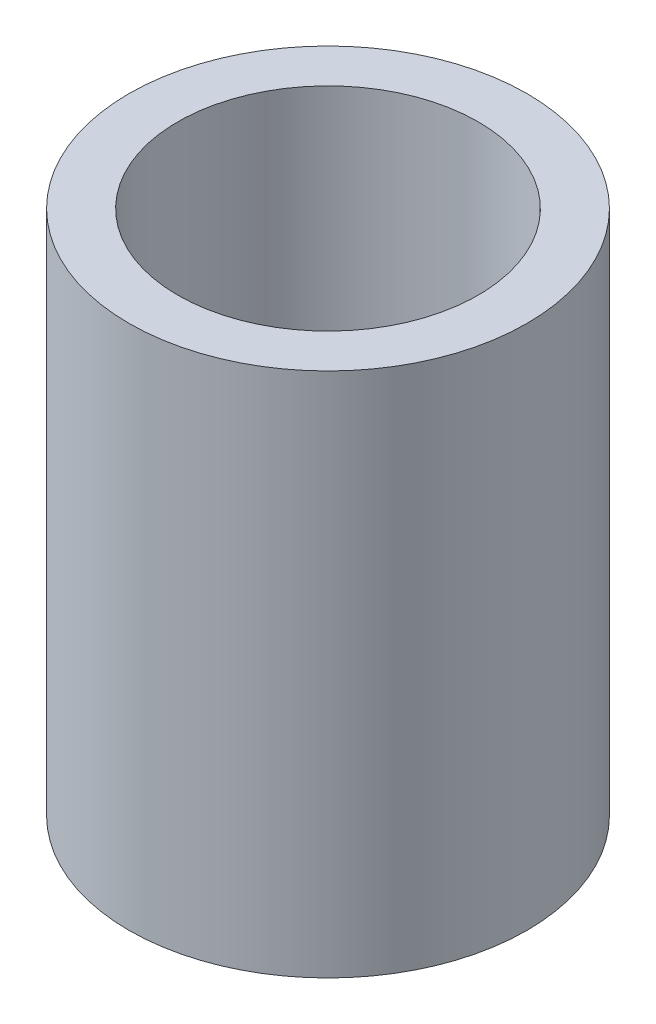
SolidWorks part; units mm, degrees
ref_plane "Front Plane" through (0, 0, 0) normal (0, 0, 1) x (1, 0, 0)
ref_plane "Top Plane" through (0, 0, 0) normal (0, 1, 0) x (1, 0, 0)
ref_plane "Right Plane" through (0, 0, 0) normal (1, 0, 0) x (0, 0, -1)
sketch "Sketch1" plane through (0, 0, 0) normal (0, 1, 0) x (1, 0, 0)
  circle A1 centre (0, 0) radius 13.25
extrude "Boss-Extrude1" add sketch "Sketch1" along normal blind 35
sketch "Sketch7" plane through (0, 0, 0) normal (0, -1, 0) x (1, 0, 0)
  circle A0 centre (0, 0) radius 10
extrude "Cut-Extrude4" cut sketch "Sketch7" against normal blind 8 contours A0
sketch "Sketch10" plane through (0, 8, 0) normal (0, -1, 0) x (1, 0, 0)
  circle A0 centre (0, 0) radius 3.485
extrude "Boss-Extrude3" add sketch "Sketch10" along normal blind 4 contours A0
sketch "Sketch11" plane through (0, 4, 0) normal (0, -1, 0) x (1, 0, 0)
  circle A3 centre (0, 0) radius 1.625
extrude "Cut-Extrude5" cut sketch "Sketch11" against normal blind 8.75
sketch "Sketch13" plane through (0, 35, 0) normal (0, 1, 0) x (1, 0, 0)
  circle A0 centre (0, 0) radius 10
extrude "Cut-Extrude6" cut sketch "Sketch13" against normal blind 18
